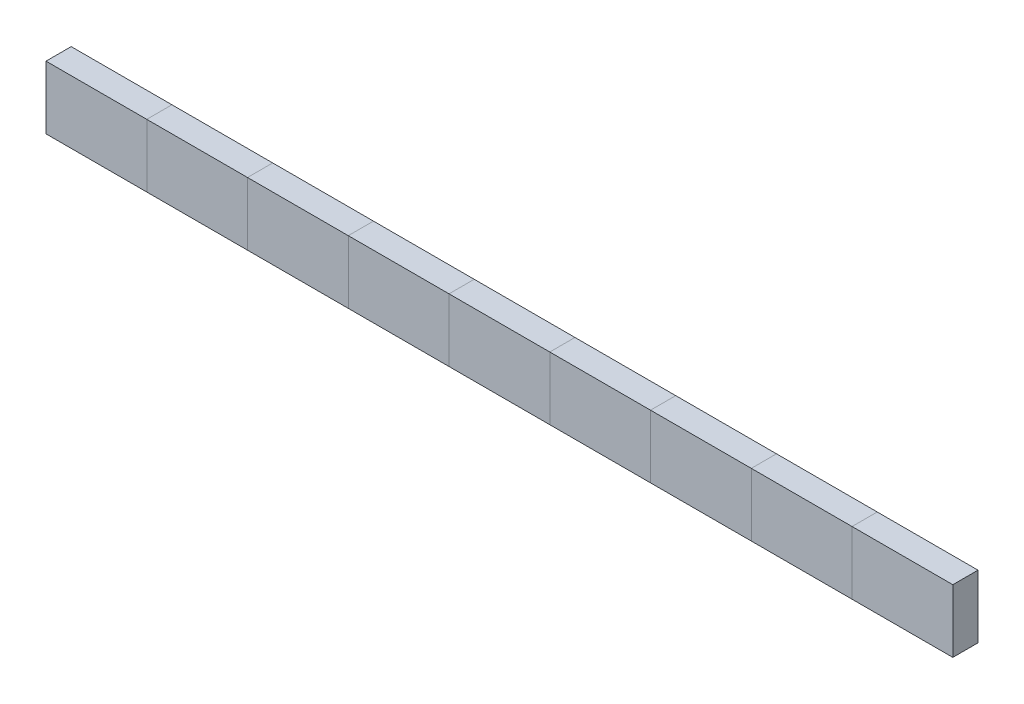
SolidWorks part; units mm, degrees
ref_plane "Front Plane" through (0, 0, 0) normal (0, 0, 1) x (1, 0, 0)
ref_plane "Top Plane" through (0, 0, 0) normal (0, 1, 0) x (1, 0, 0)
ref_plane "Right Plane" through (0, 0, 0) normal (1, 0, 0) x (0, 0, -1)
sketch "Sketch1" plane through (0, 0, 0) normal (0, 0, 1) x (1, 0, 0)
  line L3 (0, 1.27) -> (0, 0)
  line L4 (2.032, 1.27) -> (2.032, 0)
  line L22 (0, 1.27) -> (2.032, 1.27)
  line L53 (0, 0) -> (2.032, 0)
  dimension "D1" = 2.032
  dimension "D2" = 1.27
extrude "Boss-Extrude1" add sketch "Sketch1" along normal blind 0.508 contours L53 L4 L22 L3
sketch "Sketch3" plane through (2.032, 0, 0) normal (1, 0, 0) x (0, 0, -1)
  line L1 (-0.508, 1.27) -> (0, 1.27)
  line L2 (-0.508, 1.27) -> (-0.508, 0)
  line L3 (-0.508, 0) -> (0, 0)
  line L4 (0, 1.27) -> (0, 0)
extrude "Boss-Extrude3" add sketch "Sketch3" along normal blind 2.032 separate body
sketch "Sketch4" plane through (4.064, 0, 0) normal (1, 0, 0) x (0, 0, -1)
  line L1 (-0.508, 1.27) -> (0, 1.27)
  line L2 (-0.508, 1.27) -> (-0.508, 0)
  line L3 (-0.508, 0) -> (0, 0)
  line L4 (0, 1.27) -> (0, 0)
extrude "Boss-Extrude4" add sketch "Sketch4" along normal blind 2.032 separate body
sketch "Sketch5" plane through (6.096, 0, 0) normal (1, 0, 0) x (0, 0, -1)
  line L1 (-0.508, 1.27) -> (0, 1.27)
  line L2 (-0.508, 1.27) -> (-0.508, 0)
  line L3 (-0.508, 0) -> (0, 0)
  line L4 (0, 1.27) -> (0, 0)
extrude "Boss-Extrude5" add sketch "Sketch5" along normal blind 2.032 separate body
sketch "Sketch6" plane through (8.128, 0, 0) normal (1, 0, 0) x (0, 0, -1)
  line L1 (-0.508, 1.27) -> (0, 1.27)
  line L2 (-0.508, 1.27) -> (-0.508, 0)
  line L3 (-0.508, 0) -> (0, 0)
  line L4 (0, 1.27) -> (0, 0)
extrude "Boss-Extrude6" add sketch "Sketch6" along normal blind 2.032 separate body
sketch "Sketch7" plane through (10.16, 0, 0) normal (1, 0, 0) x (0, 0, -1)
  line L1 (-0.508, 1.27) -> (0, 1.27)
  line L2 (-0.508, 1.27) -> (-0.508, 0)
  line L3 (-0.508, 0) -> (0, 0)
  line L4 (0, 1.27) -> (0, 0)
extrude "Boss-Extrude7" add sketch "Sketch7" along normal blind 2.032 separate body
sketch "Sketch8" plane through (12.192, 0, 0) normal (1, 0, 0) x (0, 0, -1)
  line L1 (-0.508, 1.27) -> (0, 1.27)
  line L2 (-0.508, 1.27) -> (-0.508, 0)
  line L3 (-0.508, 0) -> (0, 0)
  line L4 (0, 1.27) -> (0, 0)
extrude "Boss-Extrude8" add sketch "Sketch8" along normal blind 2.032 separate body
sketch "Sketch9" plane through (14.224, 0, 0) normal (1, 0, 0) x (0, 0, -1)
  line L1 (-0.508, 1.27) -> (0, 1.27)
  line L2 (-0.508, 1.27) -> (-0.508, 0)
  line L3 (-0.508, 0) -> (0, 0)
  line L4 (0, 1.27) -> (0, 0)
extrude "Boss-Extrude9" add sketch "Sketch9" along normal blind 2.032 separate body
sketch "Sketch10" plane through (16.256, 0, 0) normal (1, 0, 0) x (0, 0, -1)
  line L1 (-0.508, 1.27) -> (0, 1.27)
  line L2 (-0.508, 1.27) -> (-0.508, 0)
  line L3 (-0.508, 0) -> (0, 0)
  line L4 (0, 1.27) -> (0, 0)
extrude "Boss-Extrude10" add sketch "Sketch10" along normal blind 2.032 separate body
